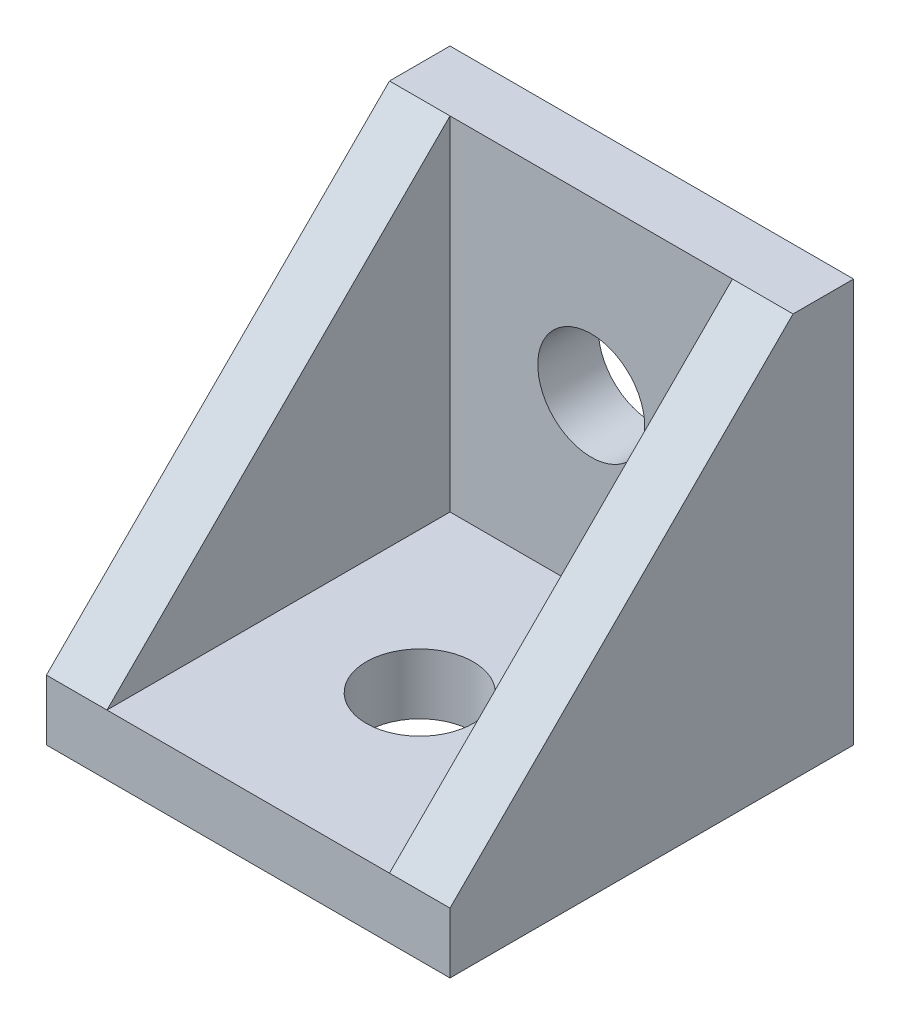
SolidWorks part; units mm, degrees
ref_plane "Front" through (0, 0, 0) normal (0, 0, 1) x (1, 0, 0)
ref_plane "Top" through (0, 0, 0) normal (0, 1, 0) x (1, 0, 0)
ref_plane "Right" through (0, 0, 0) normal (1, 0, 0) x (0, 0, -1)
sketch "Esboço1" plane through (0, 0, 0) normal (0, 0, 1) x (1, 0, 0)
  line L1 (0, 0) -> (20, 0)
  line L2 (0, 0) -> (0, 20)
  line L3 (0, 20) -> (20, 20)
  line L4 (20, 0) -> (20, 20)
  line L5 (0, 0) -> (20, 20) construction
  line L6 (0, 20) -> (20, 0) construction
  point P4 (10, 10)
  dimension "D1" = 20
  dimension "D2" = 20
extrude "Ressalto-extrusão1" add sketch "Esboço1" along normal blind 20
sketch "Esboço2" plane through (20, 0, 0) normal (1, 0, 0) x (0, 0, -1)
  line L0 (-3, 20) -> (-20, 3)
  line L1 (-20, 20) -> (0, 20) construction
  line L2 (-20, 0) -> (-20, 20) construction
  line L3 (-20, 3) -> (-20, 20)
  line L4 (-20, 20) -> (-3, 20)
  dimension "D1" = 17
  dimension "D2" = 17
extrude "Corte-extrusão1" cut sketch "Esboço2" against normal through all
sketch "Esboço3" plane through (0, 0, 20) normal (0, 0, 1) x (1, 0, 0)
  line L0 (0, 3) -> (20, 3) construction
  line L1 (3, 3) -> (17, 3)
  line L2 (3, 3) -> (3, 20)
  line L3 (3, 20) -> (17, 20)
  line L4 (17, 3) -> (17, 20)
  line L5 (3, 3) -> (17, 20) construction
  line L6 (3, 20) -> (17, 3) construction
  line L7 (0, 20) -> (20, 20) construction
  line L8 (0, 3) -> (0, 20) construction
  line L9 (20, 3) -> (20, 20) construction
  point P4 (10, 11.5)
  dimension "D1" = 3
  dimension "D2" = 3
extrude "Corte-extrusão2" cut sketch "Esboço3" against normal blind 17
sketch "Esboço4" plane through (0, 0, 0) normal (0, 0, -1) x (-1, 0, 0)
  line L0 (0, 0) -> (-20, 0) construction
  line L1 (-13, 0) -> (-7, 0)
  line L2 (-13, 0) -> (-13, 6)
  line L3 (-13, 6) -> (-7, 6)
  line L4 (-7, 0) -> (-7, 6)
  line L5 (-13, 0) -> (-7, 6) construction
  line L6 (-13, 6) -> (-7, 0) construction
  line L7 (-20, 0) -> (-20, 20) construction
  point P4 (-10, 3)
  dimension "D1" = 6
  dimension "D2" = 7
  dimension "D3" = 6
extrude "Ressalto-extrusão2" add sketch "Esboço4" along normal blind 2
sketch "Esboço5" plane through (0, 0, 0) normal (0, -1, 0) x (1, 0, 0)
  line L0 (7, -2) -> (7, 0) construction
  line L1 (13, 0) -> (7, 0)
  line L2 (13, 0) -> (13, 6)
  line L3 (13, 6) -> (7, 6)
  line L4 (7, 0) -> (7, 6)
  line L5 (13, 0) -> (7, 6) construction
  line L6 (13, 6) -> (7, 0) construction
  point P4 (10, 3)
  dimension "D1" = 6
extrude "Ressalto-extrusão3" add sketch "Esboço5" along normal blind 2
sketch "Esboço6" plane through (0, 0, 3) normal (0, 0, 1) x (1, 0, 0)
  line L0 (17, 20) -> (3, 20) construction
  circle A0 centre (10, 11.5) radius 2.65
  point P4 (10, 20)
  dimension "D1" = 5.3
  dimension "D2" = 8.5
extrude "Corte-extrusão3" cut sketch "Esboço6" against normal through all
sketch "Esboço7" plane through (0, 3, 0) normal (0, 1, 0) x (1, 0, 0)
  line L0 (3, -20) -> (17, -20) construction
  circle A0 centre (10, -11.5) radius 2.65
  point P4 (10, -20)
  dimension "D1" = 5.3
  dimension "D2" = 8.5
extrude "Corte-extrusão4" cut sketch "Esboço7" against normal through all
